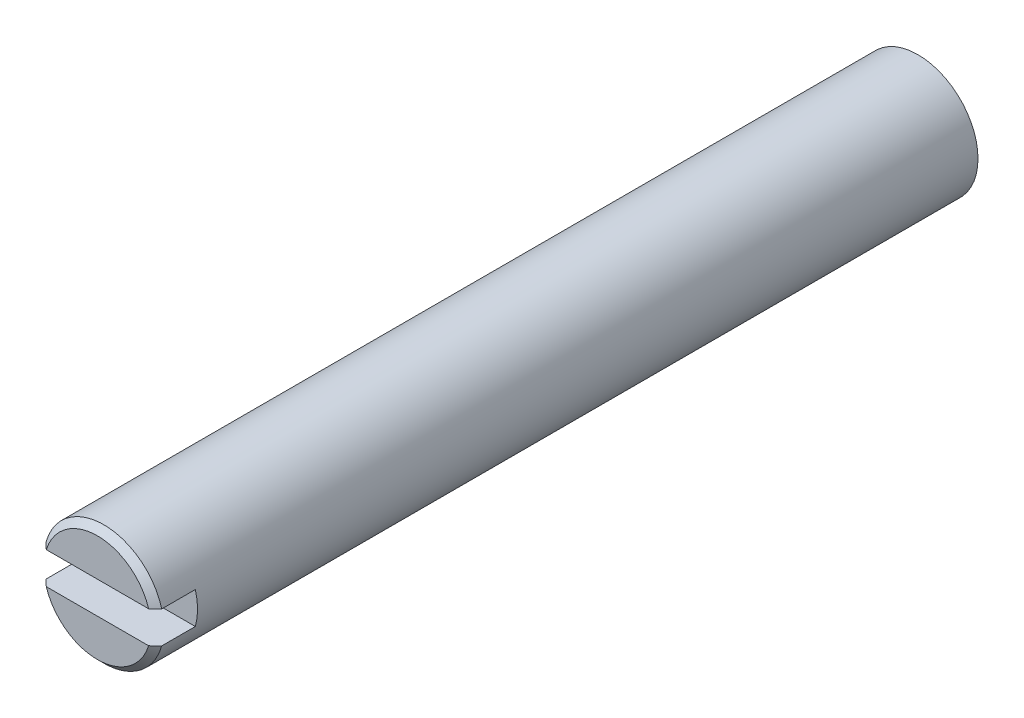
SolidWorks part; units mm, degrees
material "Plain Carbon Steel"
ref_plane "Front Plane" through (0, 0, 0) normal (0, 0, 1) x (1, 0, 0)
ref_plane "Top Plane" through (0, 0, 0) normal (0, 1, 0) x (1, 0, 0)
ref_plane "Right Plane" through (0, 0, 0) normal (1, 0, 0) x (0, 0, -1)
sketch "Sketch1" plane through (0, 0, 0) normal (0, 0, 1) x (1, 0, 0)
  circle A0 centre (0, 0) radius 4.7625
  dimension "D1" = 9.525
extrude "Boss-Extrude1" add sketch "Sketch1" along normal blind 65.1002
chamfer "Chamfer1" distance 0.508 angle 45 1 edges at (4.7625, 0, 65.1002)
sketch "Sketch2" plane through (0, 0, 65.1002) normal (0, 0, 1) x (1, 0, 0)
  line L1 (-6.35, -1.27) -> (6.35, -1.27)
  line L2 (-6.35, -1.27) -> (-6.35, 1.27)
  line L3 (-6.35, 1.27) -> (6.35, 1.27)
  line L4 (6.35, -1.27) -> (6.35, 1.27)
  line L5 (-6.35, -1.27) -> (6.35, 1.27) construction
  line L6 (-6.35, 1.27) -> (6.35, -1.27) construction
  point P0 (0, 0)
  dimension "D1" = 2.54
  dimension "D2" = 12.7
extrude "Cut-Extrude1" cut sketch "Sketch2" against normal blind 3.175
